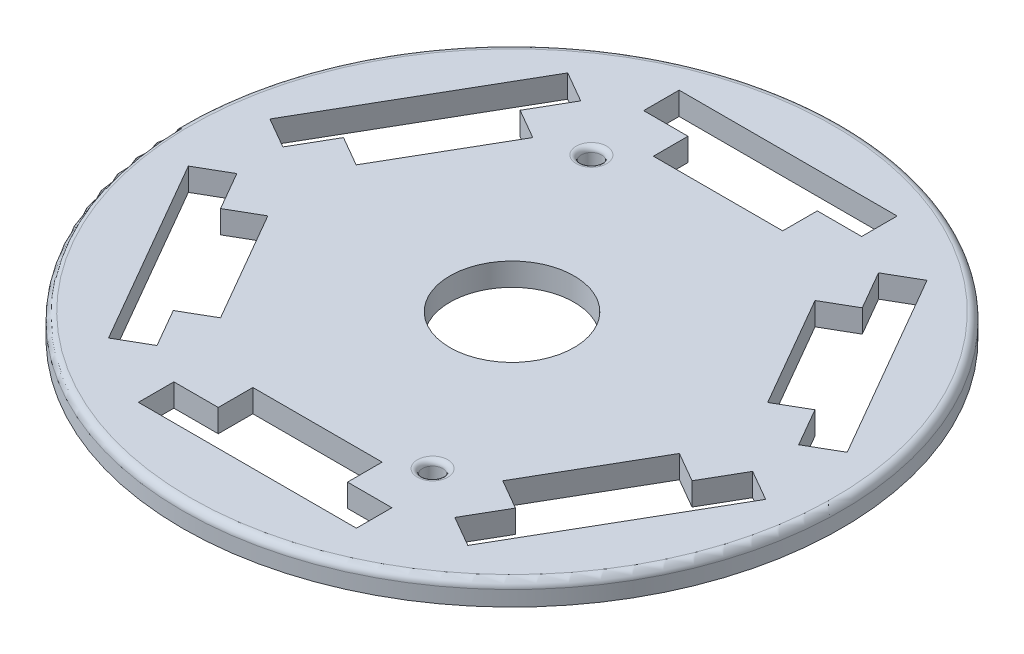
SolidWorks part; units mm, degrees
ref_plane "Front Plane" through (0, 0, 0) normal (0, 0, 1) x (1, 0, 0)
ref_plane "Top Plane" through (0, 0, 0) normal (0, 1, 0) x (1, 0, 0)
ref_plane "Right Plane" through (0, 0, 0) normal (1, 0, 0) x (0, 0, -1)
sketch "Sketch1" plane through (0, 0, 0) normal (0, 1, 0) x (1, 0, 0)
  circle A0 centre (0, 0) radius 32.5
extrude "Boss-Extrude1" add sketch "Sketch1" along normal blind 2.25
sketch "Sketch15" plane through (0.0671, 2.25, -0.5018) normal (0, 1, 0) x (1, 0, 0)
  line L0 (-13.9165, 15.3959) -> (-20.2915, 4.3541)
  line L1 (6.375, 23.25) -> (-6.375, 23.25)
  line L2 (6.375, 23.25) -> (6.375, 19.75)
  line L3 (6.375, 19.75) -> (-6.375, 19.75)
  line L4 (-6.375, 23.25) -> (-6.375, 19.75)
  line L5 (6.375, 23.25) -> (-6.375, 19.75) construction
  line L6 (6.375, 19.75) -> (-6.375, 23.25) construction
  line L7 (-23.3226, 6.1041) -> (-20.2915, 4.3541)
  line L8 (-16.9476, 17.1459) -> (-23.3226, 6.1041)
  line L9 (-16.9476, 17.1459) -> (-13.9165, 15.3959)
  line L10 (-20.2915, -4.3541) -> (-13.9165, -15.3959)
  line L11 (-16.9476, -17.1459) -> (-13.9165, -15.3959)
  line L12 (-23.3226, -6.1041) -> (-16.9476, -17.1459)
  line L13 (-23.3226, -6.1041) -> (-20.2915, -4.3541)
  line L14 (-6.375, -19.75) -> (6.375, -19.75)
  line L15 (6.375, -23.25) -> (6.375, -19.75)
  line L16 (-6.375, -23.25) -> (6.375, -23.25)
  line L17 (-6.375, -23.25) -> (-6.375, -19.75)
  line L18 (13.9165, -15.3959) -> (20.2915, -4.3541)
  line L19 (23.3226, -6.1041) -> (20.2915, -4.3541)
  line L20 (16.9476, -17.1459) -> (23.3226, -6.1041)
  line L21 (16.9476, -17.1459) -> (13.9165, -15.3959)
  line L22 (20.2915, 4.3541) -> (13.9165, 15.3959)
  line L23 (16.9476, 17.1459) -> (13.9165, 15.3959)
  line L24 (23.3226, 6.1041) -> (16.9476, 17.1459)
  line L25 (23.3226, 6.1041) -> (20.2915, 4.3541)
  point P0 (0, 21.5)
  point P28 (0, 0)
  dimension "D1" = 6
extrude "Cut-Extrude6" cut sketch "Sketch15" against normal blind 17
sketch "Sketch17" plane through (0.0671, 2.25, -0.5018) normal (0, 1, 0) x (1, 0, 0)
  line L0 (-17.7154, -22.641) -> (-28.4654, -4.0215)
  line L1 (10.75, -23.1625) -> (-10.75, -23.1625)
  line L2 (10.75, -23.1625) -> (10.75, -26.6625)
  line L3 (10.75, -26.6625) -> (-10.75, -26.6625)
  line L4 (-10.75, -23.1625) -> (-10.75, -26.6625)
  line L5 (10.75, -23.1625) -> (-10.75, -26.6625) construction
  line L6 (10.75, -26.6625) -> (-10.75, -23.1625) construction
  line L7 (-14.6843, -20.891) -> (-17.7154, -22.641)
  line L8 (-14.6843, -20.891) -> (-25.4343, -2.2715)
  line L9 (-25.4343, -2.2715) -> (-28.4654, -4.0215)
  line L10 (-28.4654, 4.0215) -> (-17.7154, 22.641)
  line L11 (-25.4343, 2.2715) -> (-28.4654, 4.0215)
  line L12 (-25.4343, 2.2715) -> (-14.6843, 20.891)
  line L13 (-14.6843, 20.891) -> (-17.7154, 22.641)
  line L14 (-10.75, 26.6625) -> (10.75, 26.6625)
  line L15 (-10.75, 23.1625) -> (-10.75, 26.6625)
  line L16 (-10.75, 23.1625) -> (10.75, 23.1625)
  line L17 (10.75, 23.1625) -> (10.75, 26.6625)
  line L18 (17.7154, 22.641) -> (28.4654, 4.0215)
  line L19 (14.6843, 20.891) -> (17.7154, 22.641)
  line L20 (14.6843, 20.891) -> (25.4343, 2.2715)
  line L21 (25.4343, 2.2715) -> (28.4654, 4.0215)
  line L22 (28.4654, -4.0215) -> (17.7154, -22.641)
  line L23 (25.4343, -2.2715) -> (28.4654, -4.0215)
  line L24 (25.4343, -2.2715) -> (14.6843, -20.891)
  line L25 (14.6843, -20.891) -> (17.7154, -22.641)
  point P0 (0, -24.9125)
  point P6 (-21.5749, -12.4563)
  point P13 (-21.5749, 12.4563)
  point P18 (0, 24.9125)
  point P23 (21.5749, 12.4563)
  point P28 (21.5749, -12.4563)
  point P33 (0, 0)
  dimension "D1" = 6
extrude "Cut-Extrude7" cut sketch "Sketch17" against normal blind 12
sketch "Sketch19" plane through (0, 2.25, 0) normal (0, 1, 0) x (1, 0, 0)
  circle A0 centre (-9.4763, 17.3066) radius 1
  circle A1 centre (9.4763, -17.3066) radius 1
  point P7 (0, 0)
  dimension "D1" = 2
extrude "Cut-Extrude9" cut sketch "Sketch19" against normal blind 16
sketch "Sketch21" plane through (0, 2.25, 0) normal (0, 1, 0) x (1, 0, 0)
  circle A0 centre (0, 0) radius 6.125
ref_plane "Plane1" through (0, 17, 0) normal (-1, 0, 0) x (0, 0, -1)
ref_plane "Plane2" through (0, 17, 0) normal (-1, 0, 0) x (0, 0, -1)
ref_plane "Plane3" through (0, 17, 0) normal (-1, 0, 0) x (0, 0, -1)
ref_plane "Plane4" through (0, 17, 0) normal (-1, 0, 0) x (0, 0, -1)
fillet "Fillet4" radius 0.5 2 edges at (-9.4763, 2.25, -16.3066) (9.4763, 2.25, 18.3066)
fillet "Fillet5" radius 0.5 2 edges at (-9.4763, 0, -16.3066) (9.4763, 0, 18.3066)
extrude "Cut-Extrude11" cut sketch "Sketch21" against normal blind 13 contours A0
fillet "Fillet8" radius 0.75 1 edges at (0, 2.25, 32.5)
